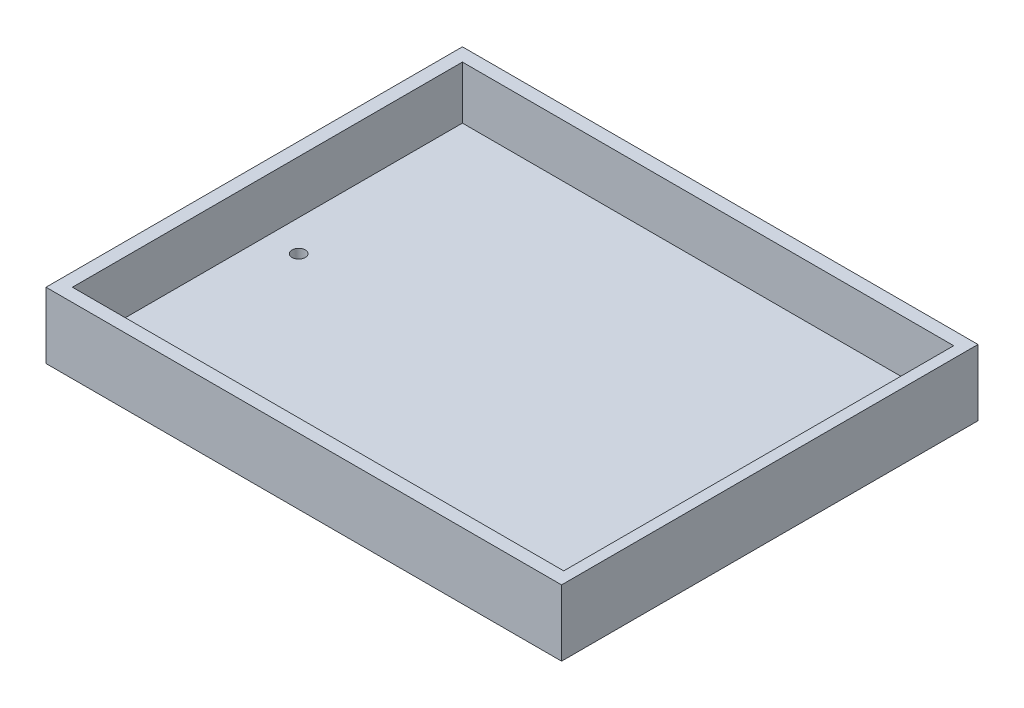
SolidWorks part; units mm, degrees
ref_plane "Front Plane" through (0, 0, 0) normal (0, 0, 1) x (1, 0, 0)
ref_plane "Top Plane" through (0, 0, 0) normal (0, 1, 0) x (1, 0, 0)
ref_plane "Right Plane" through (0, 0, 0) normal (1, 0, 0) x (0, 0, -1)
sketch "Sketch2" plane through (0, 0, 0) normal (0, 1, 0) x (1, 0, 0)
  line L1 (-36.6667, 29.3301) -> (41.3333, 29.3301)
  line L2 (-36.6667, 29.3301) -> (-36.6667, -33.6699)
  line L3 (-36.6667, -33.6699) -> (41.3333, -33.6699)
  line L4 (41.3333, 29.3301) -> (41.3333, -33.6699)
  dimension "D1" = 63
  dimension "D2" = 78
extrude "Boss-Extrude1" add sketch "Sketch2" along normal blind 10
sketch "Sketch3" plane through (0, 10, 0) normal (0, 1, 0) x (1, 0, 0)
  line L0 (-36.6667, 29.3301) -> (-36.6667, -33.6699) construction
  line L1 (-34.6667, 27.3301) -> (39.661, 27.3301)
  line L2 (-34.6667, 27.3301) -> (-34.6667, -31.6699)
  line L3 (-34.6667, -31.6699) -> (39.661, -31.6699)
  line L4 (39.661, 27.3301) -> (39.661, -31.6699)
  line L5 (41.3333, 29.3301) -> (-36.6667, 29.3301) construction
  line L6 (-36.6667, -33.6699) -> (41.3333, -33.6699) construction
  line L7 (41.3333, -33.6699) -> (41.3333, 29.3301) construction
  dimension "D1" = 2
  dimension "D2" = 2
  dimension "D3" = 2
  dimension "D4" = 1.6723
extrude "Cut-Extrude1" cut sketch "Sketch3" against normal blind 8 contours L2 L1 L4 L3
sketch "Sketch6" plane through (0, 0, 0) normal (0, -1, 0) x (1, 0, 0)
  line L0 (-160.0838, 79.3681) -> (-64.0593, 24.2557) construction
  line L1 (32.6908, -22.5844) -> (33.0922, -22.5844)
  line L2 (32.4907, -22.3557) -> (32.9671, -22.2637)
  line L3 (32.4907, -21.8623) -> (32.9611, -21.9356)
  line L4 (32.6908, -21.5976) -> (33.0821, -21.5976)
  line L5 (32.6908, -22.5844) -> (32.3346, -22.5122)
  line L6 (32.6908, -21.5976) -> (32.3346, -21.6746)
  line L7 (32.4907, -22.3557) -> (32.3201, -22.2458)
  line L8 (32.4907, -21.8623) -> (32.3346, -21.9353)
  line L9 (32.3346, -22.5122) -> (32.3201, -22.2458)
  line L10 (32.3346, -21.9353) -> (32.3346, -21.6746)
  line L11 (32.0863, -19.8252) -> (33.1374, -21.5141)
  line L12 (33.2503, -21.0885) -> (32.3584, -19.6169)
  line L13 (32.0863, -19.8252) -> (29.2267, -19.1963)
  line L14 (32.3584, -19.6169) -> (30.1578, -19.1329)
  line L15 (29.2267, -19.1963) -> (30.1578, -19.1329)
  line L16 (32.2321, -24.6781) -> (33.2262, -23.0146)
  line L17 (32.0863, -24.4076) -> (33.1374, -22.6511)
  line L18 (30.3764, -24.9662) -> (32.2321, -24.6781)
  line L19 (32.0863, -24.4076) -> (29.2267, -24.9662)
  line L20 (29.2267, -24.9662) -> (30.3764, -24.9662)
  line L21 (33.2503, -21.0885) -> (33.2067, -19.2508)
  line L22 (33.2067, -19.2508) -> (30.914, -17.3585)
  line L23 (30.914, -17.3585) -> (32.1286, -17.9837)
  line L24 (32.1286, -17.9837) -> (33.521, -19.1329)
  line L25 (33.521, -19.1329) -> (33.521, -21.2082)
  line L26 (33.2262, -23.0146) -> (33.1374, -24.9662)
  line L27 (33.1374, -24.9662) -> (30.8165, -26.649)
  line L28 (30.8165, -26.649) -> (32.0863, -26.0164)
  line L29 (32.0863, -26.0164) -> (33.3724, -25.0839)
  line L30 (33.3724, -25.0839) -> (33.5269, -22.9575)
  line L31 (33.5269, -22.9575) -> (34.2647, -25.1463)
  line L32 (34.2647, -25.1463) -> (36.8808, -26.7333)
  line L33 (36.8808, -26.7333) -> (36.1915, -26.0164)
  line L34 (36.1915, -26.0164) -> (34.5986, -24.9662)
  line L35 (34.5986, -24.9662) -> (33.9446, -23.1486)
  line L36 (33.521, -21.2082) -> (34.2875, -18.9596)
  line L37 (34.2875, -18.9596) -> (36.8944, -17.4586)
  line L38 (36.8944, -17.4586) -> (36.1915, -18.2157)
  line L39 (36.1915, -18.2157) -> (34.5986, -19.1329)
  line L40 (34.5986, -19.1329) -> (33.9046, -21.1278)
  line L41 (33.9446, -23.1486) -> (35.2438, -24.6781)
  line L42 (35.2438, -24.6781) -> (38.9801, -25.2482)
  line L43 (38.9801, -25.2482) -> (37.8178, -24.735)
  line L44 (37.8178, -24.735) -> (35.579, -24.3935)
  line L45 (35.579, -24.3935) -> (34.2516, -22.9722)
  line L46 (33.9046, -21.1278) -> (35.2792, -19.5771)
  line L47 (35.2792, -19.5771) -> (39.1152, -18.9681)
  line L48 (39.1152, -18.9681) -> (37.8657, -19.5008)
  line L49 (37.8657, -19.5008) -> (35.531, -19.8715)
  line L50 (35.531, -19.8715) -> (34.3292, -21.2273)
  line L51 (34.6311, -21.463) -> (34.3292, -21.2273)
  line L52 (34.6316, -22.7017) -> (34.2516, -22.9722)
  arc A1 (34.6316, -22.7017) -> (34.6311, -21.463) centre (36.263, -22.0818) ccw
  arc A3 (33.0922, -22.5844) -> (33.1374, -22.6511) centre (33.9046, -22.0826) ccw
  arc A4 (32.9611, -21.9356) -> (32.9671, -22.2637) centre (33.9046, -22.0826) ccw
  arc A5 (33.1374, -21.5141) -> (33.0821, -21.5976) centre (33.9046, -22.0826) ccw
extrude "Cut-Extrude2" cut sketch "Sketch6" against normal blind 0.5
sketch "Sketch7" plane through (0, 0, 0) normal (0, -1, 0) x (1, 0, 0)
  circle A0 centre (-29.9466, 2.1699) radius 1
  point P2 (-29.9466, 2.1699)
extrude "Cut-Extrude4" cut sketch "Sketch7" against normal blind 10
